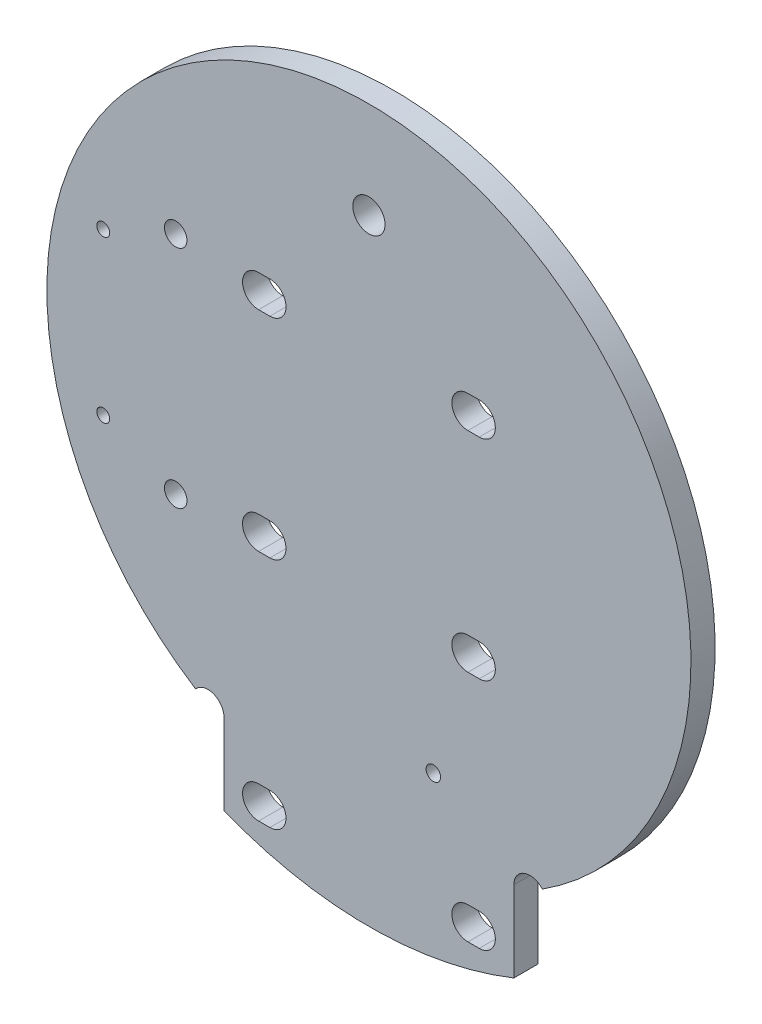
SolidWorks part; units mm, degrees
ref_plane "Спереди" through (0, 0, 0) normal (0, 0, 1) x (1, 0, 0)
ref_plane "Сверху" through (0, 0, 0) normal (0, 1, 0) x (1, 0, 0)
ref_plane "Справа" through (0, 0, 0) normal (1, 0, 0) x (0, 0, -1)
sketch "Эскиз1" plane through (0, 0, 0) normal (0, 0, 1) x (1, 0, 0)
  line L0 (21, 12.5) -> (21, 7.482)
  line L2 (39, 7.482) -> (39, 12.5)
  line L3 (13.3247, 13.5) -> (49.0789, 13.5) construction
  arc A0 (19.2351, 13.1442) -> (40.7649, 13.1442) centre (30, 30) cw
  arc A1 (19.2351, 13.1442) -> (21, 12.5) centre (20, 12.5) cw
  arc A2 (40.7649, 13.1442) -> (39, 12.5) centre (40, 12.5) ccw
  arc A3 (39, 7.482) -> (21, 7.482) centre (30, 30) cw
  dimension "D1" = 20
  dimension "D2" = 24.25
  dimension "D4" = 1
  dimension "D5" = 16.5
  dimension "D7" = 30
  dimension "D3" = 18
  dimension "D6" = 30
extrude "Бобышка-Вытянуть1" add sketch "Эскиз1" along normal blind 1.5
sketch "Эскиз2" plane through (0, 0, 1.5) normal (0, 0, 1) x (1, 0, 0)
  line L0 (23.85, 36.5) -> (23.15, 36.5) construction
  line L1 (23.85, 35.5) -> (23.15, 35.5)
  line L2 (23.85, 37.5) -> (23.15, 37.5)
  line L3 (36.85, 36.5) -> (36.15, 36.5) construction
  line L4 (36.85, 35.5) -> (36.15, 35.5)
  line L5 (36.85, 37.5) -> (36.15, 37.5)
  line L6 (23.85, 23.5) -> (23.15, 23.5) construction
  line L7 (23.85, 22.5) -> (23.15, 22.5)
  line L8 (23.85, 24.5) -> (23.15, 24.5)
  line L9 (36.85, 23.5) -> (36.15, 23.5) construction
  line L10 (36.85, 22.5) -> (36.15, 22.5)
  line L11 (36.85, 24.5) -> (36.15, 24.5)
  line L12 (23.85, 9) -> (23.15, 9) construction
  line L13 (23.85, 8) -> (23.15, 8)
  line L14 (23.85, 10) -> (23.15, 10)
  line L15 (36.85, 9) -> (36.15, 9) construction
  line L16 (36.85, 8) -> (36.15, 8)
  line L17 (36.85, 10) -> (36.15, 10)
  arc A0 (23.85, 35.5) -> (23.85, 37.5) centre (23.85, 36.5) ccw
  arc A1 (23.15, 37.5) -> (23.15, 35.5) centre (23.15, 36.5) ccw
  arc A2 (36.85, 35.5) -> (36.85, 37.5) centre (36.85, 36.5) ccw
  arc A3 (36.15, 37.5) -> (36.15, 35.5) centre (36.15, 36.5) ccw
  arc A4 (23.85, 22.5) -> (23.85, 24.5) centre (23.85, 23.5) ccw
  arc A5 (23.15, 24.5) -> (23.15, 22.5) centre (23.15, 23.5) ccw
  arc A6 (36.85, 22.5) -> (36.85, 24.5) centre (36.85, 23.5) ccw
  arc A7 (36.15, 24.5) -> (36.15, 22.5) centre (36.15, 23.5) ccw
  arc A8 (23.85, 8) -> (23.85, 10) centre (23.85, 9) ccw
  arc A9 (23.15, 10) -> (23.15, 8) centre (23.15, 9) ccw
  arc A10 (36.85, 8) -> (36.85, 10) centre (36.85, 9) ccw
  arc A11 (36.15, 10) -> (36.15, 8) centre (36.15, 9) ccw
  arc A12 (40.7649, 13.1442) -> (19.2351, 13.1442) centre (30, 30) ccw construction
  circle A13 centre (34, 16) radius 0.45
  circle A14 centre (30, 44) radius 1
  circle A15 centre (13.5, 35) radius 0.4
  circle A16 centre (13.5, 25) radius 0.4
  circle A17 centre (18, 37) radius 0.7
  circle A18 centre (18, 23) radius 0.7
  point P2 (23.5, 36.5)
  point P11 (36.5, 36.5)
  point P18 (23.5, 23.5)
  point P25 (36.5, 23.5)
  point P32 (23.5, 9)
  point P39 (36.5, 9)
  dimension "D13" = 6.5
  dimension "D15" = 6.5
  dimension "D2" = 14
  dimension "D3" = 4
  dimension "D4" = 0.9
  dimension "D7" = 0
  dimension "D8" = 14
  dimension "D9" = 2
  dimension "D10" = 16.5
  dimension "D11" = 5
  dimension "D12" = 10
  dimension "D18" = 0.8
  dimension "D19" = 12
  dimension "D20" = 7
  dimension "D21" = 14
  dimension "D22" = 1.4
  dimension "D5" = 0.7
  dimension "D6" = 2
  dimension "D14" = 13
  dimension "D16" = 13
  dimension "D17" = 14.5
extrude "Вырез-Вытянуть1" cut sketch "Эскиз2" against normal through all
